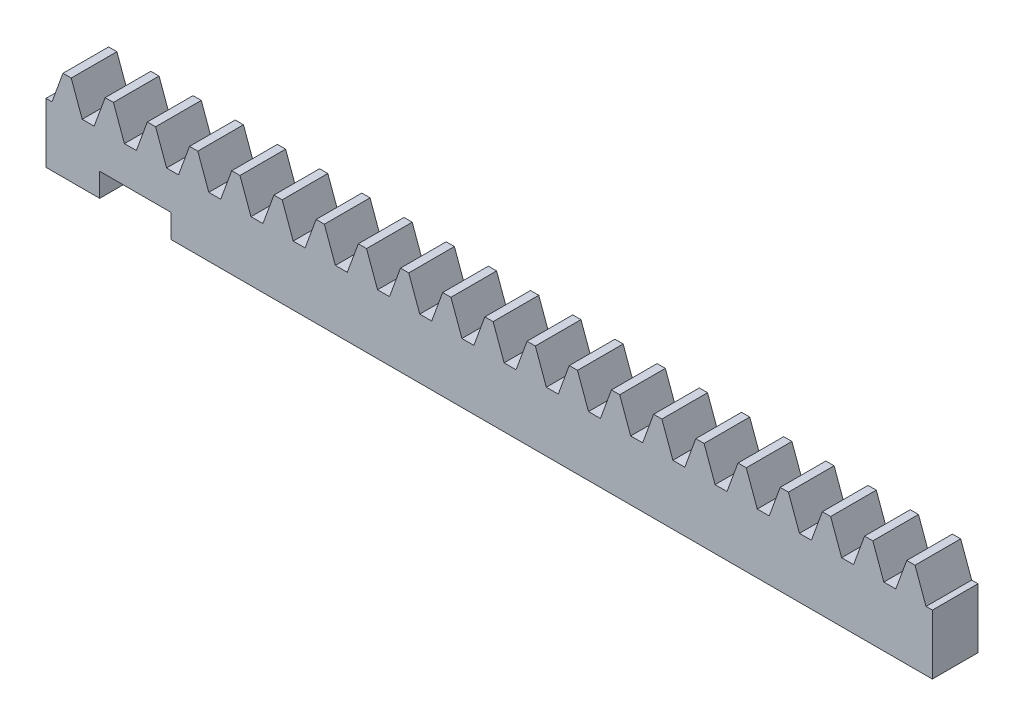
SolidWorks part; units mm, degrees
ref_plane "Plane1" through (0, 0, 0) normal (0, 0, 1) x (1, 0, 0)
ref_plane "Plane2" through (0, 0, 0) normal (0, 1, 0) x (1, 0, 0)
ref_plane "Plane3" through (0, 0, 0) normal (1, 0, 0) x (0, 0, -1)
sketch "HoldingSke" plane through (0, 0, 0) normal (0, 1, 0) x (1, 0, 0)
  line L0 (0, 0) -> (0.1392, 0.9903)
  line L1 (-15, 0) -> (100, 0) construction
  line L2 (0, 0) -> (-2.1039, 2.3779)
  line L3 (0, 0) -> (-11.863, 4.5341)
  line L4 (0, 0) -> (7.9495, 3.3743)
  line L5 (0, 0) -> (-23.7986, -8.8762)
  line L6 (0, 0) -> (-10.5278, -7.1032)
  line L9 (-71.009, 38.7566) -> (-8.9893, 61.3299)
  line L10 (-76.2, 3.3779) -> (-70.5, 3.3779)
  line L11 (0, 0) -> (-3.4, 0)
  line L12 (-76.2, 101.6) -> (-76.162, 101.6)
  line L13 (24.9733, 27.94) -> (52.9518, 28.4284)
  line L14 (24.9733, 27.94) -> (24.9743, 27.94)
  line L15 (24.9733, 27.94) -> (100.4006, 29.5858)
  circle A0 centre (0, 0) radius 19.05
  circle A1 centre (0, 0) radius 2.85
  circle A2 centre (0, 0) radius 12.7
  dimension "MPH" = 5.7
  dimension "Diameter" = 38.1
  dimension "Num_teeth" = 23
  dimension "Pitch" = 1
  dimension "Width" = 3.4
  dimension "Show_teeth" = 998
  dimension "Thickness" = 12.7
  dimension "Ap" = 20
  dimension "Pitch_height" = 5.7
  dimension "Backlash" = 0.038
  dimension "Addendum_fac" = 1
  dimension "Dedendum_fac" = 1.25
  dimension "Clearance_fac" = 0.25
  dimension "Dedendum_add" = 0.001
  dimension "Length" = 66
  dimension "Module" = 1
sketch "BlankSke" plane through (0, 0, 0) normal (0, 0, 1) x (1, 0, 0)
  line L1 (0, 0) -> (66, 0)
  line L2 (0, 0) -> (0, 6.7)
  line L3 (0, 6.7) -> (66, 6.7)
  line L4 (66, 0) -> (66, 6.7)
  dimension "Length" = 66
  dimension "Blank_height" = 6.7
extrude "Blank" add sketch "BlankSke" against normal blind 3.4
sketch "TooCutSkeIll" plane through (0, 0, 0) normal (0, 0, 1) x (1, 0, 0)
  line L0 (-1.2538, 6.6737) -> (-0.5045, 4.6152)
  line L1 (-0.2687, 4.45) -> (0.2687, 4.45)
  line L2 (0.5045, 4.6152) -> (1.2538, 6.6737)
  line L3 (66, 6.7) -> (0, 6.7) construction
  line L4 (0, 0) -> (0, 64.897) construction
  line L5 (-13.208, 5.7) -> (12.954, 5.7) construction
  line L6 (0, 0) -> (66, 0) construction
  line L7 (0.8994, 5.7) -> (0.8994, 48.7463) construction
  line L8 (-0.8994, 5.7) -> (-0.8994, 48.7463) construction
  line L9 (1.2914, 6.7) -> (1.2914, 6.7254)
  line L10 (-1.2914, 6.7) -> (-1.2914, 6.7254)
  line L11 (-1.2914, 6.7254) -> (1.2914, 6.7254)
  arc A0 (0.2687, 4.45) -> (0.5045, 4.6152) centre (0.2687, 4.701) ccw
  arc A1 (-0.5045, 4.6152) -> (-0.2687, 4.45) centre (-0.2687, 4.701) ccw
  arc A2 (1.2914, 6.7) -> (1.2538, 6.6737) centre (1.2914, 6.66) ccw
  arc A3 (-1.2538, 6.6737) -> (-1.2914, 6.7) centre (-1.2914, 6.66) ccw
  dimension "Root_fillet" = 0.251
  dimension "Break_rad" = 0.04
  dimension "Pitch_height" = 5.7
  dimension "Gap_width" = 1.7988
  dimension "Dedendum" = 1.25
  dimension "Addendum_plus" = 1.0254
  dimension "Pressure_angle" = 20
extrude "ToothCutIll" [suppressed] cut sketch "TooCutSkeIll" against normal through all
sketch "TooCutSkeSim" plane through (0, 0, 0) normal (0, 0, 1) x (1, 0, 0)
  line L0 (0.4444, 4.45) -> (-0.4444, 4.45)
  line L1 (1.2726, 6.7254) -> (0.4444, 4.45)
  line L2 (0, 17.4625) -> (0, 53.467) construction
  line L3 (1.2726, 6.7254) -> (-1.2726, 6.7254)
  line L6 (-1.2726, 6.7254) -> (-0.4444, 4.45)
  line L9 (-0.8994, 5.7) -> (0.8994, 5.7) construction
  line L10 (0, 0) -> (66, 0) construction
  line L11 (0.8994, 5.7) -> (0.8994, 53.467) construction
  line L12 (-0.8994, 5.7) -> (-0.8994, 53.467) construction
  dimension "Pitch_height" = 5.7
  dimension "Pressure_angle" = 20
  dimension "Gap_width" = 1.7988
  dimension "Dedendum" = 1.25
  dimension "Addendum_plus" = 1.0254
extrude "ToothCutSim" cut sketch "TooCutSkeSim" against normal through all
pattern_linear "TeethCuts" count 22 spacing 3.1416 along (1, 0, 0) of "ToothCutIll", "ToothCutSim"
sketch "notch-sketch" plane through (0, 0, 0) normal (0, 0, 1) x (1, 0, 0)
  line L0 (0, 0) -> (66, 0) construction
  line L1 (4, 0) -> (9.3, 0)
  line L2 (4, 0) -> (4, 1.75)
  line L3 (4, 1.75) -> (9.3, 1.75)
  line L4 (9.3, 0) -> (9.3, 1.75)
  line L5 (0, 4.45) -> (0, 0) construction
  dimension "D1" = 5.3
  dimension "D2" = 1.75
  dimension "D3" = 4
extrude "notch" cut sketch "notch-sketch" against normal through all
equation "' \"Module@HoldingSke\" = 6.35"
equation "' \"Num_teeth@HoldingSke\" = 12"
equation "' \"Ap@HoldingSke\" =  20"
equation "' \"Width@HoldingSke\" = 0.25 * 25.4"
equation "' \"Show_teeth@HoldingSke\" = 500"
equation "' \"Backlash@HoldingSke\" = 0.009 * 25.4"
equation "' \"Addendum_fac@HoldingSke\" = 1.0"
equation "' \"Dedendum_fac@HoldingSke\" = 1.25"
equation "' \"Dedendum_add@HoldingSke\" = 0.00005 * 25.4"
equation "' \"Clearance_fac@HoldingSke\" = 0.25"
equation "' \"Pitch_height@HoldingSke\" = 1 * 25.4"
equation "' \"Length@HoldingSke\" = 4.71 * 25.4"
equation "\"Pitch@HoldingSke\" = 1 / \"Module@HoldingSke\""
equation "\"MPH@HoldingSke\" = \"Dedendum_fac@HoldingSke\" / \"Pitch@HoldingSke\" + 2 * \"Dedendum_add@HoldingSke\" + 0.002 * 25.4"
equation "\"MPH@HoldingSke\" = ((sgn( \"MPH@HoldingSke\" - \"Pitch_height@HoldingSke\")+1)*( \"MPH@HoldingSke\" - \"Pitch_height@HoldingSke\"))/2 + \"Pitch_height@HoldingSke\""
equation "\"Blank_height@BlankSke\" = \"Pitch_height@HoldingSke\" + \"Addendum_fac@HoldingSke\"  / \"Pitch@HoldingSke\" "
equation "\"Length@BlankSke\" =  \"Length@HoldingSke\""
equation "\"Face_width@Blank\" = \"Width@HoldingSke\""
equation "\"Pressure_angle@TooCutSkeIll\" = \"Ap@HoldingSke\""
equation "\"Addendum_plus@TooCutSkeIll\" =  \"Addendum_fac@HoldingSke\"  / \"Pitch@HoldingSke\" + 0.001 *25.4"
equation "\"Dedendum@TooCutSkeIll\" = \"Dedendum_fac@HoldingSke\"  / \"Pitch@HoldingSke\""
equation "\"Pitch_height@TooCutSkeIll\" =  \"MPH@HoldingSke\""
equation "\"Gap_width@TooCutSkeIll\" = 3.14159265 / 2 / \"Pitch@HoldingSke\" + 6 * \"Backlash@HoldingSke\""
equation "\"Pressure_angle@TooCutSkeSim\" = \"Ap@HoldingSke\""
equation "\"Addendum_plus@TooCutSkeSim\" =  \"Addendum_fac@HoldingSke\"  / \"Pitch@HoldingSke\" + 0.001 * 25.4"
equation "\"Dedendum@TooCutSkeSim\" = \"Dedendum_fac@HoldingSke\"  / \"Pitch@HoldingSke\""
equation "\"Pitch_height@TooCutSkeSim\" =  \"MPH@HoldingSke\""
equation "\"Gap_width@TooCutSkeSim\" = 3.14159265 / 2 / \"Pitch@HoldingSke\" + 6 * \"Backlash@HoldingSke\""
equation "\"Root_fillet@TooCutSkeIll\" = \"Clearance_fac@HoldingSke\" / \"Pitch@HoldingSke\" + \"Dedendum_add@HoldingSke\""
equation "\"Break_rad@TooCutSkeIll\" = 0.02 / \"Pitch@HoldingSke\" * 2"
equation "\"Linear_pitch@TeethCuts\" = 3.14159265 / \"Pitch@HoldingSke\""
equation "\"Num_teeth@HoldingSke\" = int( ( \"Length@HoldingSke\" + 0 ) / (3.14159265 / \"Pitch@HoldingSke\")) + 0.9999  + 1"
equation " \"Num_teeth@TeethCuts\" = int( \"Show_teeth@HoldingSke\" ) + 1"
equation " \"Num_teeth@TeethCuts\" = ((sgn( \"Num_teeth@TeethCuts\" - \"Num_teeth@HoldingSke\" )-1)*( \"Num_teeth@TeethCuts\" - \"Num_teeth@HoldingSke\" ))/-2+ \"Num_teeth@HoldingSke\""
equation " \"Num_teeth@TeethCuts\" = ((sgn( \"Num_teeth@TeethCuts\" - 2.0)+1)*( \"Num_teeth@TeethCuts\" - 2.0))/2 +2.0"
